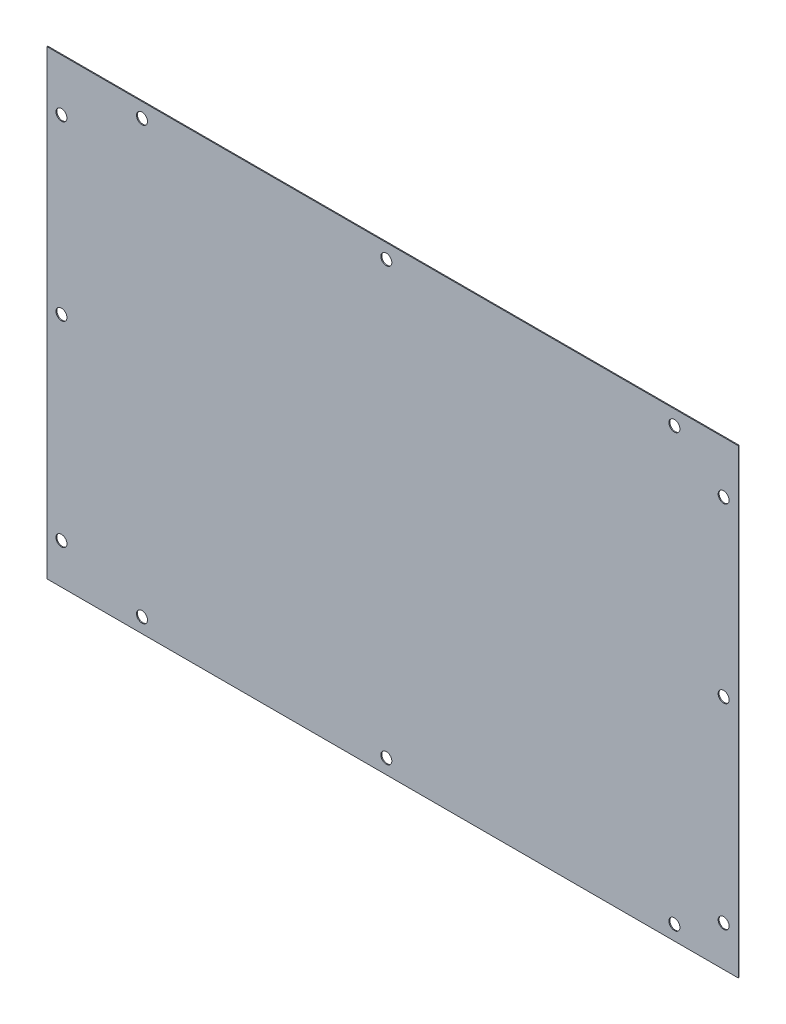
SolidWorks part; units mm, degrees
ref_plane "Alzado" through (0, 0, 0) normal (0, 0, 1) x (1, 0, 0)
ref_plane "Planta" through (0, 0, 0) normal (0, 1, 0) x (1, 0, 0)
ref_plane "Vista lateral" through (0, 0, 0) normal (1, 0, 0) x (0, 0, -1)
sketch "Croquis1" plane through (0, 0, 0) normal (0, 0, 1) x (1, 0, 0)
  line L0 (25.4, 400) -> (25.4, 0) construction
  line L1 (0, 400) -> (600, 400)
  line L2 (0, 400) -> (0, 0)
  line L3 (0, 0) -> (600, 0)
  line L4 (600, 400) -> (600, 0)
  line L5 (574.6, 400) -> (574.6, 0) construction
  line L6 (25.4, 374.6) -> (574.6, 374.6) construction
  line L7 (25.4, 25.4) -> (574.6, 25.4) construction
  line L8 (18.7867, 387.3) -> (12.7, 387.3) construction
  line L9 (12.7, 387.3) -> (12.7, 380.1826) construction
  line L10 (581.5853, 12.7) -> (587.3, 12.7) construction
  line L11 (587.3, 12.7) -> (587.3, 19.1562) construction
  circle A0 centre (82.592, 387.3) radius 4.7625
  circle A1 centre (294.6, 387.3) radius 4.7625
  circle A2 centre (544.6, 387.3) radius 4.7625
  circle A3 centre (12.7, 355) radius 4.7625
  circle A4 centre (12.7, 205) radius 4.7625
  circle A5 centre (12.7, 35) radius 4.7625
  circle A6 centre (82.592, 12.7) radius 4.7625
  circle A7 centre (294.6, 12.7) radius 4.7625
  circle A8 centre (544.6, 12.7) radius 4.7625
  circle A9 centre (587.3, 355) radius 4.7625
  circle A10 centre (587.3, 205) radius 4.7625
  circle A11 centre (587.3, 35) radius 4.7625
  point P43 (0, 0)
  point P44 (0, 0)
  point P45 (0, 0)
  point P46 (0, 0)
  point P47 (0, 0)
  point P48 (0, 0)
  point P49 (0, 0)
  point P50 (0, 0)
  point P51 (0, 0)
  point P52 (0, 0)
  point P53 (266.1899, 386.3687)
  point P54 (179.6267, 387.7649)
  point P55 (447.5289, 287.6839)
  point P56 (0, 0)
  point P57 (473.997, 237.5779)
  point P58 (495.787, 234.1733)
  point P59 (581.5853, 225.321)
  point P60 (588.3947, 79.6002)
  point P61 (589.0756, 91.1761)
  point P62 (590.1491, 7.8304)
  point P63 (589.2586, 14.2866)
  dimension "D17" = 9.525
  dimension "D1" = 600
  dimension "D2" = 400
  dimension "D3" = 25.4
  dimension "D4" = 25.4
  dimension "D5" = 25.4
  dimension "D6" = 25.4
  dimension "D7" = 12.7
  dimension "D8" = 12.7
  dimension "D9" = 57.192
  dimension "D10" = 30
  dimension "D11" = 250
  dimension "D12" = 45
  dimension "D13" = 150
  dimension "D14" = 320
  dimension "D15" = 12.7
  dimension "D16" = 12.7
extrude "Saliente-Extruir1" add sketch "Croquis1" along normal blind 0.7937
